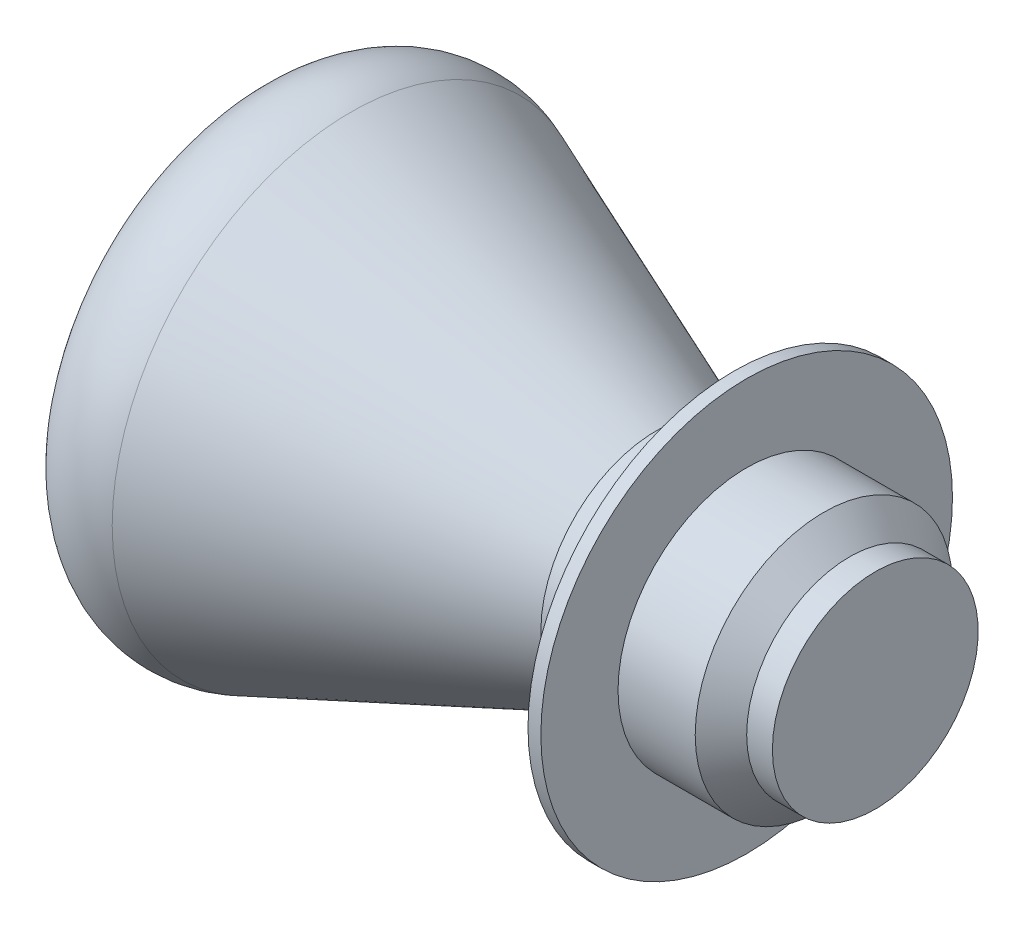
SolidWorks part; units mm, degrees
ref_plane "Front Plane" through (0, 0, 0) normal (0, 0, 1) x (1, 0, 0)
ref_plane "Top Plane" through (0, 0, 0) normal (0, 1, 0) x (1, 0, 0)
ref_plane "Right Plane" through (0, 0, 0) normal (1, 0, 0) x (0, 0, -1)
sketch "Sketch2" plane through (0, 0, 0) normal (0, 0, 1) x (1, 0, 0)
  line L1 (5.5, 0) -> (5.5, 4)
  line L2 (5.5, 4) -> (4.5, 4)
  line L3 (4.5, 4) -> (3.5, 5)
  line L4 (3.5, 5) -> (0.5, 5)
  line L5 (0.5, 5) -> (0.5, 8)
  line L6 (0.5, 8) -> (0, 8)
  line L7 (0, 8) -> (0, 5)
  line L8 (0, 5) -> (-2, 5)
  line L14 (-2, 5) -> (-2, 0)
  line L15 (-2, 0) -> (5.5, 0)
  dimension "D1" = 5
  dimension "D2" = 1
  dimension "D3" = 1
  dimension "D4" = 1
  dimension "D5" = 3
  dimension "D6" = 0.5
  dimension "D7" = 2
  dimension "D8" = 3
revolve "Revolve1" add sketch "Sketch2" angle 360 about L15
sketch "Sketch3" plane through (0, 0, 0) normal (0, 0, 1) x (1, 0, 0)
  line L0 (0, 0) -> (-25.1298, 0) construction
sketch "Sketch4" plane through (0, 0, 0) normal (0, 0, 1) x (1, 0, 0)
  line L0 (0, 4.5) -> (-3, 4.5)
  line L1 (0, 8) -> (0, -8) construction
  line L2 (-3, 4.5) -> (-14.8796, 9.2829)
  line L3 (0, 4.5) -> (0, 0)
  line L4 (0, 0) -> (-19.8584, 0)
  line L5 (0, 0) -> (-25.1298, 0) construction
  line L7 (0, 5) -> (-2, 5) construction
  arc A0 (-14.8796, 9.2829) -> (-18.8972, 7.2788) centre (-16, 6.5) ccw
  arc A1 (-19.8584, 0) -> (-18.8972, 7.2788) centre (8.1816, 0) cw
  point P12 (-20.5016, 8)
  point P13 (-23.2152, 6.1881)
  point P16 (-18.8512, 7.433)
  point P17 (-16.7046, 9.2829)
  point P18 (-18.8464, 7.4475)
  point P19 (-17.2571, 9.2829)
  point P20 (-18.9056, 7.2467)
  point P21 (0, 0)
  dimension "D2" = 3
  dimension "D6" = 28.04
  dimension "D1" = 16
  dimension "D3" = 2
  dimension "D4" = 3
  dimension "D5" = 0.5
revolve "Revolve2" add sketch "Sketch4" angle 360 about L4
